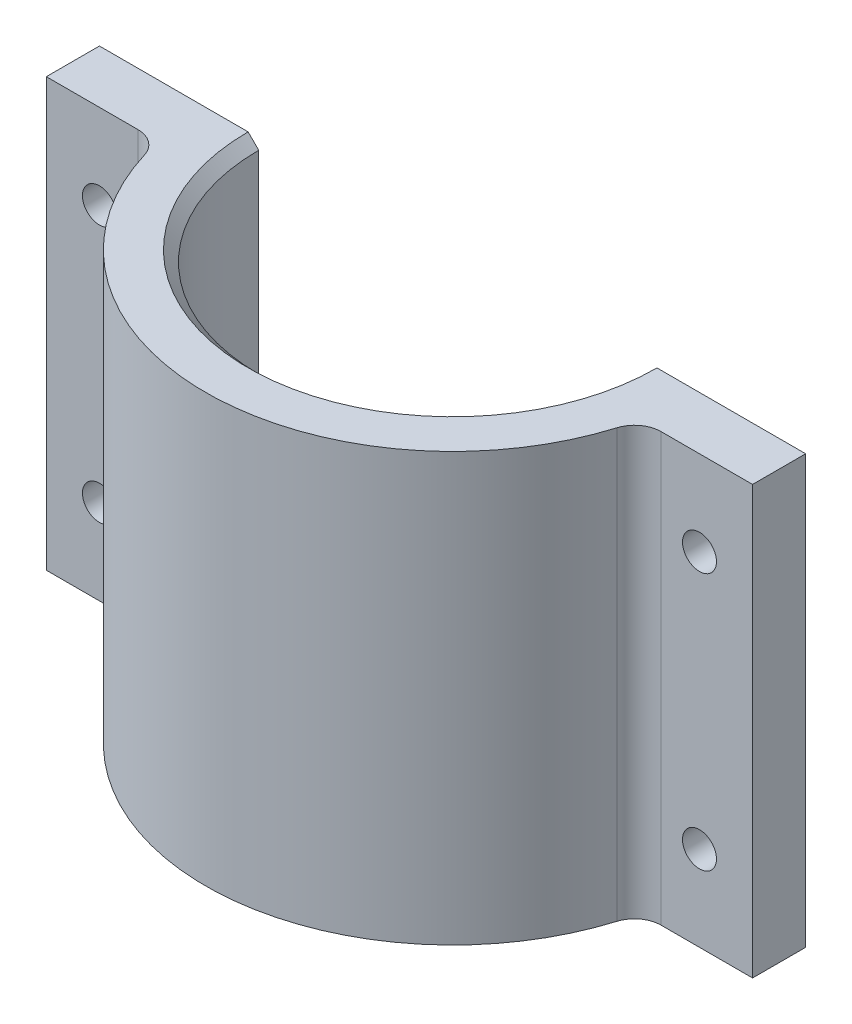
SolidWorks part; units mm, degrees
material "PBT Общее назначение"
ref_plane "Спереди" through (0, 0, 0) normal (0, 0, 1) x (1, 0, 0)
ref_plane "Сверху" through (0, 0, 0) normal (0, 1, 0) x (1, 0, 0)
ref_plane "Справа" through (0, 0, 0) normal (1, 0, 0) x (0, 0, -1)
sketch "Эскиз1" plane through (0, 0, 0) normal (0, 1, 0) x (1, 0, 0)
  line L0 (-23.25, 0) -> (-18.25, 0)
  line L1 (18.25, 0) -> (23.25, 0)
  arc A0 (-18.25, 0) -> (18.25, 0) centre (0, 0) ccw
  arc A1 (-23.25, 0) -> (23.25, 0) centre (0, 0) ccw
  dimension "D1" = 36.5
  dimension "D2" = 5
  dimension "D3" = 46.5
extrude "Бобышка-Вытянуть1" add sketch "Эскиз1" along normal blind 40.25
sketch "Эскиз2" plane through (0, 0, 0) normal (0, 0, -1) x (-1, 0, 0)
  line L0 (-23.25, 40.25) -> (-23.25, 0)
  line L1 (-23.25, 40.25) -> (-33.25, 40.25)
  line L2 (-23.25, 0) -> (-33.25, 0)
  line L3 (-33.25, 40.25) -> (-33.25, 0)
  line L4 (23.25, 40.25) -> (23.25, 0)
  line L5 (23.25, 40.25) -> (33.25, 40.25)
  line L6 (23.25, 0) -> (33.25, 0)
  line L7 (33.25, 40.25) -> (33.25, 0)
  dimension "D1" = 10
  dimension "D2" = 10
extrude "Бобышка-Вытянуть2" add sketch "Эскиз2" against normal blind 5 separate body
sketch "Эскиз3" plane through (0, 40.25, 0) normal (0, 1, 0) x (1, 0, 0)
  line L0 (23.25, -5) -> (23.25, 0) construction
  line L1 (23.25, -5) -> (23.25, 0)
  line L2 (-23.25, -5) -> (-23.25, 0) construction
  line L3 (-23.25, -5) -> (-23.25, 0)
  line L4 (23.25, -5) -> (33.25, -5) construction
  line L5 (23.25, -5) -> (24.6336, -5)
  line L6 (-33.25, -5) -> (-23.25, -5) construction
  line L7 (-24.6336, -5) -> (-23.25, -5)
  arc A0 (-23.25, 0) -> (23.25, 0) centre (0, 0) ccw construction
  arc A1 (-23.25, 0) -> (-22.242, -6.7718) centre (0, 0) ccw
  arc A2 (24.6336, -5) -> (22.242, -6.7718) centre (24.6336, -7.5) ccw
  arc A3 (-22.242, -6.7718) -> (-24.6336, -5) centre (-24.6336, -7.5) ccw
  arc A4 (22.242, -6.7718) -> (23.25, 0) centre (0, 0) ccw
  dimension "D1" = 5
  dimension "D2" = 5
extrude "Бобышка-Вытянуть3" add sketch "Эскиз3" against normal up to surface (40.25 mm away) up to face at (0, 0, 10.375)
chamfer "Фаска1" distance 1 angle 45 1 edges at (0, 40.25, 18.25)
sketch "Эскиз4" plane through (0, 0, 0) normal (0, 0, -1) x (-1, 0, 0)
  circle A0 centre (28.25, 32.25) radius 1.6 construction
  circle A1 centre (28.25, 32.25) radius 1.6
  circle A2 centre (28.25, 8) radius 1.6 construction
  circle A3 centre (28.25, 8) radius 1.6
  circle A4 centre (-28.25, 32.25) radius 1.6 construction
  circle A5 centre (-28.25, 32.25) radius 1.6
  circle A6 centre (-28.25, 8) radius 1.6 construction
  circle A7 centre (-28.25, 8) radius 1.6
extrude "Вырез-Вытянуть1" cut sketch "Эскиз4" against normal through all
